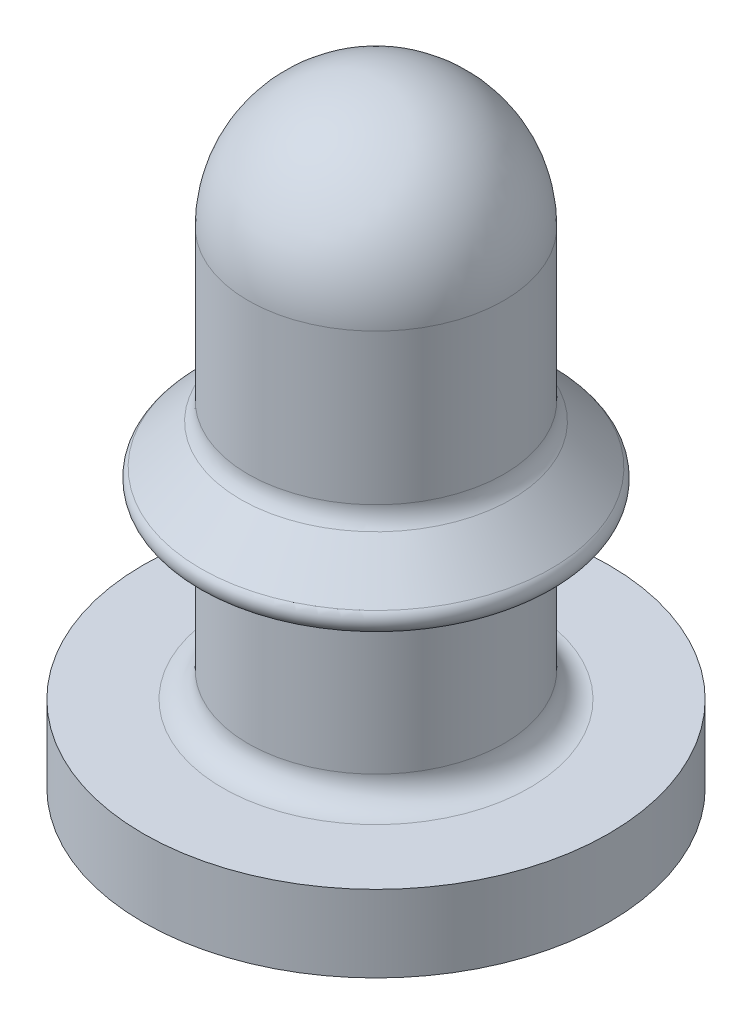
SolidWorks part; units mm, degrees
ref_plane "Front Plane" through (0, 0, 0) normal (0, 0, 1) x (1, 0, 0)
ref_plane "Top Plane" through (0, 0, 0) normal (0, 1, 0) x (1, 0, 0)
ref_plane "Right Plane" through (0, 0, 0) normal (1, 0, 0) x (0, 0, -1)
sketch "Sketch1" plane through (0, 0, 0) normal (0, 1, 0) x (1, 0, 0)
  circle A0 centre (0, 0) radius 2.5
  dimension "D1" = 5
extrude "Boss-Extrude1" add sketch "Sketch1" along normal blind 12
sketch "Sketch6" plane through (0, 0, 0) normal (0, -1, 0) x (1, 0, 0)
  circle A0 centre (0, 0) radius 4.55
  dimension "D1" = 9.1
extrude "Boss-Extrude3" add sketch "Sketch6" against normal blind 1.5
sketch "Sketch8" plane through (0, 0, 0) normal (0, 0, 1) x (1, 0, 0)
  line L0 (2.5, 6.3536) -> (3.4268, 5.4268)
  line L1 (2.5, 1.5) -> (2.5, 12) construction
  line L2 (3.25, 5) -> (2.5, 5)
  line L3 (2.5, 5) -> (2.5, 6.3536)
  line L5 (4.55, 1.5) -> (-4.55, 1.5) construction
  line L6 (0, 0) -> (0, 12) construction
  line L7 (-4.55, 0) -> (4.55, 0) construction
  line L8 (2.5, 12) -> (-2.5, 12) construction
  arc A0 (3.25, 5) -> (3.4268, 5.4268) centre (3.25, 5.25) ccw
  dimension "D3" = 0.5
  dimension "D4" = 1
  dimension "D1" = 3.5
  dimension "D2" = 45
revolve "Revolve1" add sketch "Sketch8" angle 360 about L6
sketch "Sketch2" plane through (0, 0, 0) normal (0, -1, 0) x (1, 0, 0)
  circle A0 centre (0, 0) radius 1
  dimension "D1" = 2
extrude "Cut-Extrude1" cut sketch "Sketch2" against normal blind 10
draft "Draft1" type of draft neutral plane draft angle 1 faces to draft 1 face at (0, 10, -1) neutral plane through (0, 10, 0) neutral plane normal (0, -1, 0) parameters "D1"=1
sketch "Sketch7" plane through (0, 0, 0) normal (0, 0, 1) x (1, 0, 0)
  line L0 (2.5, 6.3536) -> (2.5, 12) construction
  line L1 (2.5, 12) -> (-2.5, 12) construction
  line L4 (0, 9.5) -> (0, 12) construction
  line L5 (2.5, 9.5) -> (3.0807, 9.5)
  line L6 (3.0807, 9.5) -> (3.0807, 12.5807)
  line L7 (3.0807, 12.5807) -> (0, 12.5807)
  line L8 (0, 12.5807) -> (0, 12)
  arc A0 (2.5, 9.5) -> (0, 12) centre (0, 9.5) ccw
  dimension "D1" = 3.0807
revolve "Cut-Revolve3" cut sketch "Sketch7" angle 360 about L4
sketch "Sketch3" plane through (0, 10, 0) normal (0, -1, 0) x (1, 0, 0)
  line L0 (1.151, 0.2338) -> (0.746, 0)
  line L1 (0.746, 0) -> (1.151, -0.2338)
  line L2 (0, 0) -> (1.1746, 0) construction
  line L3 (1.151, 0.2338) -> (1.151, -0.2338) construction
  line L6 (-0.373, -1.1138) -> (-0.373, -0.6461)
  line L7 (-0.373, -0.6461) -> (-0.778, -0.8799)
  line L10 (-0.373, -1.1138) -> (-0.778, -0.8799) construction
  line L11 (-0.778, 0.8799) -> (-0.373, 0.6461)
  line L14 (-0.373, 0.6461) -> (-0.373, 1.1138)
  line L15 (-0.778, 0.8799) -> (-0.373, 1.1138) construction
  arc A1 (-0.778, -0.8799) -> (-0.373, -1.1138) centre (0, 0) ccw
  arc A2 (-0.373, 1.1138) -> (-0.778, 0.8799) centre (0, 0) ccw
  circle A7 centre (0, 0) radius 1.1746 construction
  arc A8 (1.151, -0.2338) -> (1.151, 0.2338) centre (0, 0) ccw
  circle A9 centre (0, 0) radius 1 construction
  point P16 (0, 0)
  dimension "D1" = 0.254
extrude "Boss-Extrude2" add sketch "Sketch3" along normal up to surface (10 mm away)
sketch "ref_for_revolve" plane through (0, 0, 0) normal (0, -1, 0) x (1, 0, 0)
  circle A0 centre (0, 0) radius 1.1746 construction
sketch "Sketch4" plane through (0, 0, 0) normal (0, 0, 1) x (1, 0, 0)
  line L1 (1.1746, 0) -> (0.746, 0.5107)
  line L2 (0.746, 0.5107) -> (0, 0.5107)
  line L4 (0, 0.5107) -> (0, 0)
  line L5 (0.746, 0.5107) -> (0.746, 0) construction
  line L6 (0.746, 0) -> (1.1746, 0) construction
  line L7 (1.1746, 0) -> (0, 0)
  line L8 (-0.373, 0) -> (1.151, 0) construction
  line L9 (-1.1746, 0) -> (1.1746, 0) construction
  dimension "D1" = 50
revolve "Cut-Revolve1" cut sketch "Sketch4" angle 360 about L4
fillet "Fillet1" radius 0.5 3 edges at (0, 1.5, -2.5) (0, 5, -2.5) (0, 6.3536, -2.5)
